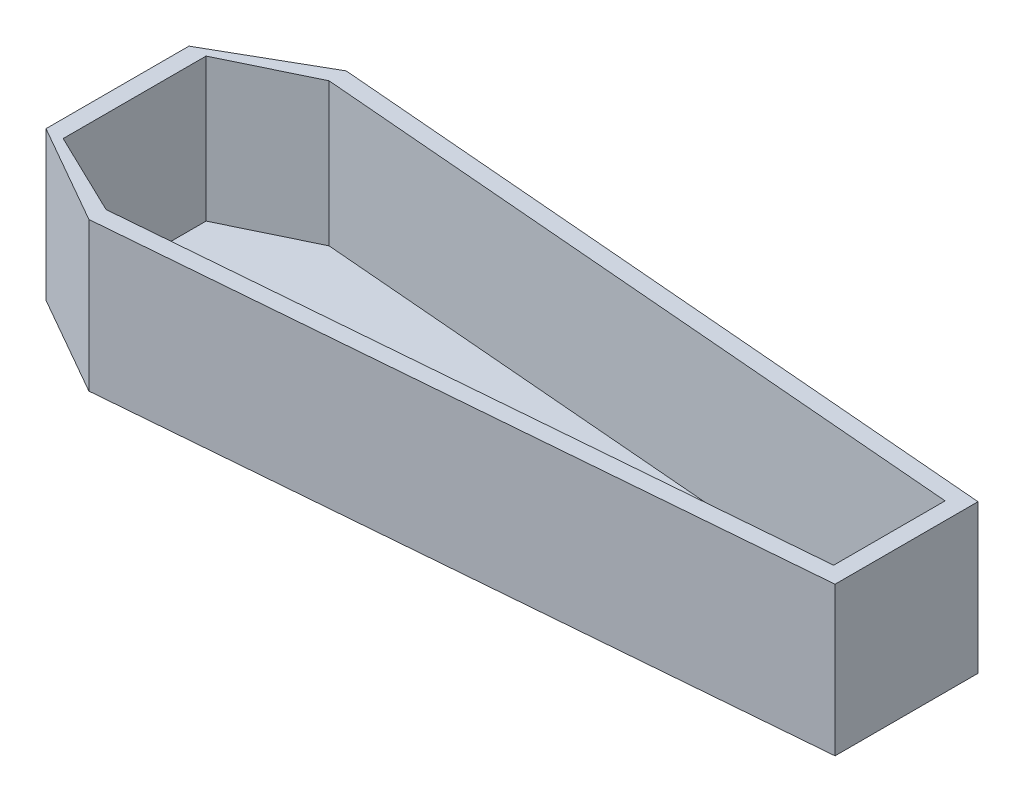
SolidWorks part; units mm, degrees
ref_plane "Front Plane" through (0, 0, 0) normal (0, 0, 1) x (1, 0, 0)
ref_plane "Top Plane" through (0, 0, 0) normal (0, 1, 0) x (1, 0, 0)
ref_plane "Right Plane" through (0, 0, 0) normal (1, 0, 0) x (0, 0, -1)
sketch "Sketch1" plane through (0, 0, 0) normal (0, 1, 0) x (1, 0, 0)
  line L0 (-183.6841, 29.0619) -> (-183.6841, -20.9381)
  line L1 (-183.6841, -20.9381) -> (-148.6841, -40.9381)
  line L2 (-148.6841, -40.9381) -> (92.3073, -20.9381)
  line L3 (-183.6841, 29.0619) -> (-148.6841, 49.0619)
  line L4 (-148.6841, 49.0619) -> (92.3073, 29.0619)
  line L5 (92.3073, 23.0619) -> (92.3073, -20.9381)
  line L7 (-183.6841, 29.0619) -> (-177.6841, 29.0619)
  line L8 (-177.6841, 29.0619) -> (-148.6841, 43.0619)
  line L10 (-177.6841, -20.9381) -> (-177.6841, 29.0619)
  line L12 (-177.6841, -20.9381) -> (-148.6841, -34.9381)
  line L13 (92.3073, 29.0619) -> (92.3073, 23.0619)
  line L14 (-148.6841, 43.0619) -> (86.3073, 23.5598)
  line L15 (92.3073, -20.9381) -> (92.3073, -14.9381)
  line L16 (-148.6841, -34.9381) -> (86.3073, -15.4361)
  line L17 (86.3073, -14.9381) -> (86.3073, -15.4361)
  line L18 (86.3073, 23.0619) -> (86.3073, 23.5598)
  line L19 (86.3073, 23.0619) -> (86.3073, -14.9381)
  dimension "D1" = 50
  dimension "D2" = 35
  dimension "D3" = 20
  dimension "D4" = 35
  dimension "D5" = 20
  dimension "D6" = 20
  dimension "D7" = 20
  dimension "D8" = 50
  dimension "D9" = 6
  dimension "D10" = 6
  dimension "D11" = 6
  dimension "D12" = 6
  dimension "D13" = 6
  dimension "D14" = 6
  dimension "D15" = 6
extrude "Boss-Extrude5" add sketch "Sketch1" along normal blind 50
sketch "Sketch3" plane through (0, 0, 0) normal (0, -1, 0) x (1, 0, 0)
  line L0 (-183.6841, 20.9381) -> (-183.6841, -29.0619)
  line L1 (-183.6841, -29.0619) -> (-148.6841, -49.0619)
  line L2 (-148.6841, -49.0619) -> (92.3073, -29.0619)
  line L3 (92.3073, -29.0619) -> (92.3073, 20.9381)
  line L4 (92.3073, 20.9381) -> (-148.6841, 40.9381)
  line L5 (-148.6841, 40.9381) -> (-183.6841, 20.9381)
extrude "Boss-Extrude6" add sketch "Sketch3" along normal blind 2
